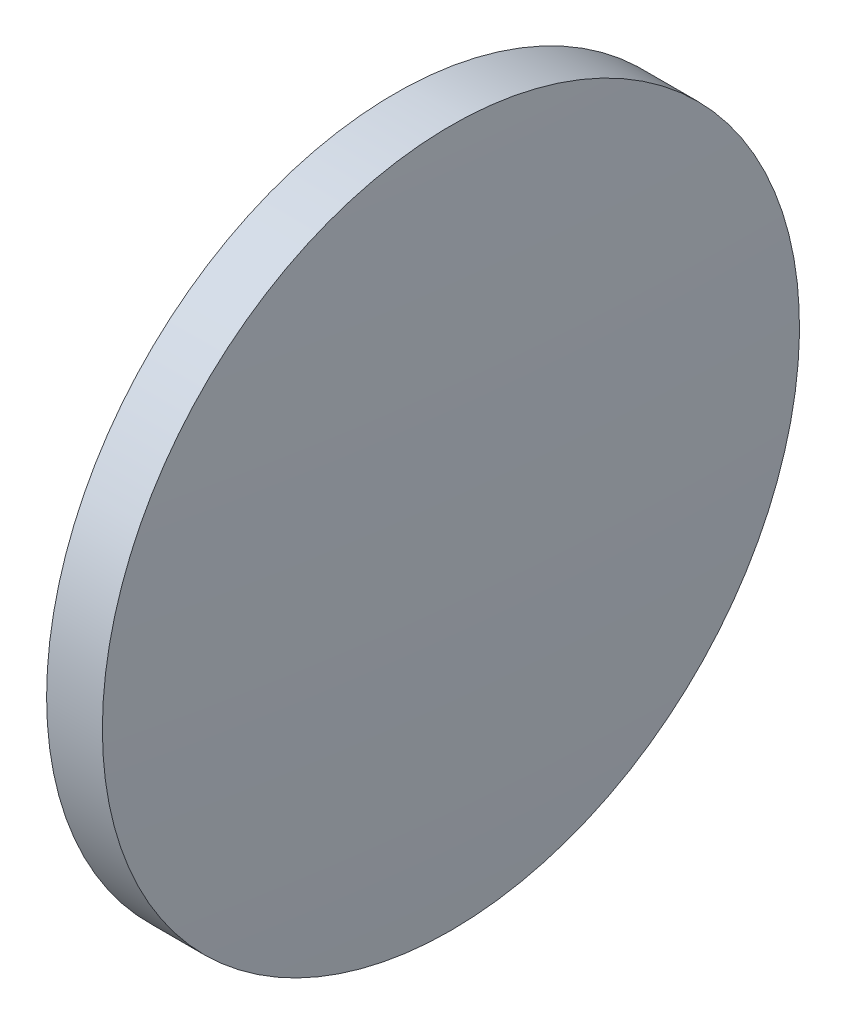
SolidWorks part; units mm, degrees
ref_plane "前视基准面" through (0, 0, 0) normal (0, 0, 1) x (1, 0, 0)
ref_plane "上视基准面" through (0, 0, 0) normal (0, 1, 0) x (1, 0, 0)
ref_plane "右视基准面" through (0, 0, 0) normal (1, 0, 0) x (0, 0, -1)
sketch "草图1" plane through (0, 0, 0) normal (0, 0, 1) x (1, 0, 0)
  line L0 (589.4087, 81.3732) -> (598.9968, 81.3732) construction
  line L1 (591.7743, 81.3732) -> (591.7743, 93.8732)
  line L2 (594.0743, 81.3732) -> (591.7743, 81.3732)
  line L5 (591.7743, 93.8732) -> (593.7743, 93.8732)
  arc A0 (594.0743, 81.3732) -> (593.7743, 93.8732) centre (333.5077, 81.3732) ccw
revolve "旋转1" add sketch "草图1" angle 360 about L0
